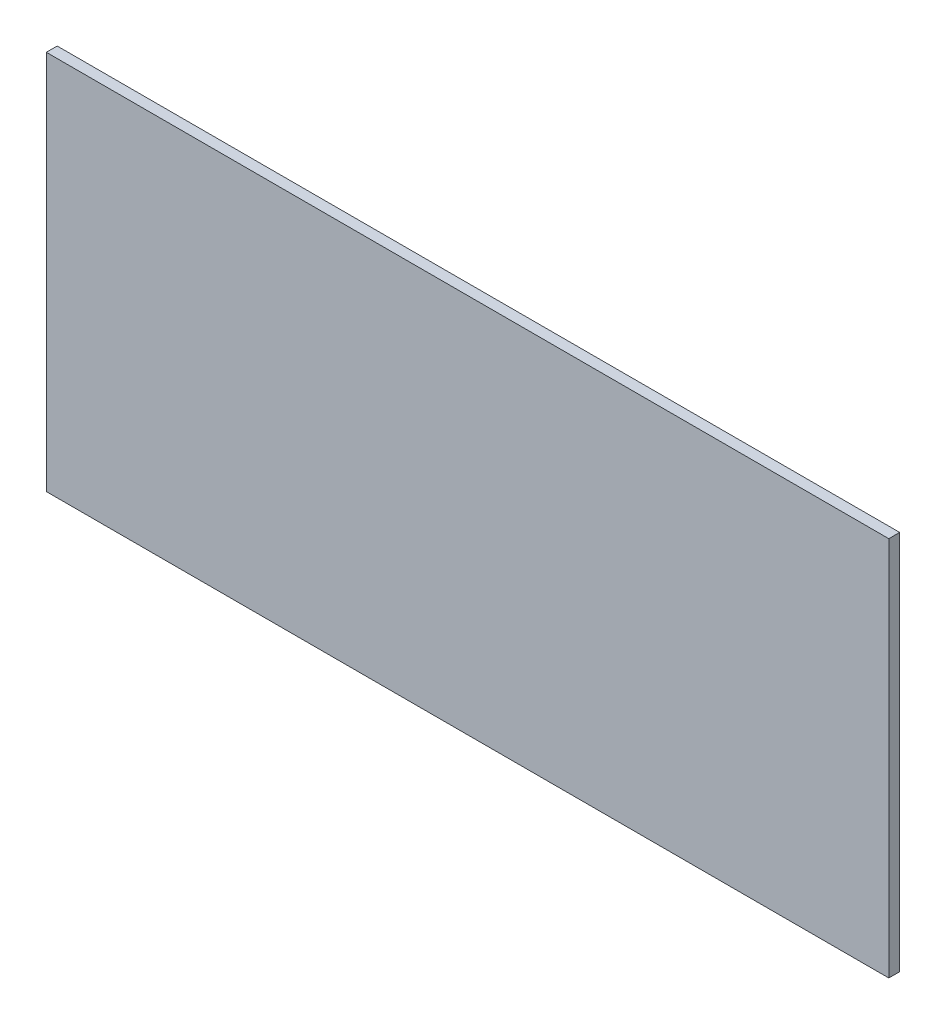
SolidWorks part; units mm, degrees
material "PC High Viscosity"
ref_plane "Front Plane" through (0, 0, 0) normal (0, 0, 1) x (1, 0, 0)
ref_plane "Top Plane" through (0, 0, 0) normal (0, 1, 0) x (1, 0, 0)
ref_plane "Right Plane" through (0, 0, 0) normal (1, 0, 0) x (0, 0, -1)
sketch "Sketch2" plane through (0, 0, 0) normal (0, 0, 1) x (1, 0, 0)
  line L1 (-77.5, 35) -> (77.5, 35)
  line L2 (-77.5, 35) -> (-77.5, -35)
  line L3 (-77.5, -35) -> (77.5, -35)
  line L4 (77.5, 35) -> (77.5, -35)
  line L5 (0, -35) -> (0, 35) construction
  line L6 (-77.5, 0) -> (77.5, 0) construction
  point P0 (0, 0)
  dimension "D1" = 155
  dimension "D2" = 70
extrude "Boss-Extrude1" add sketch "Sketch2" along normal blind 2
